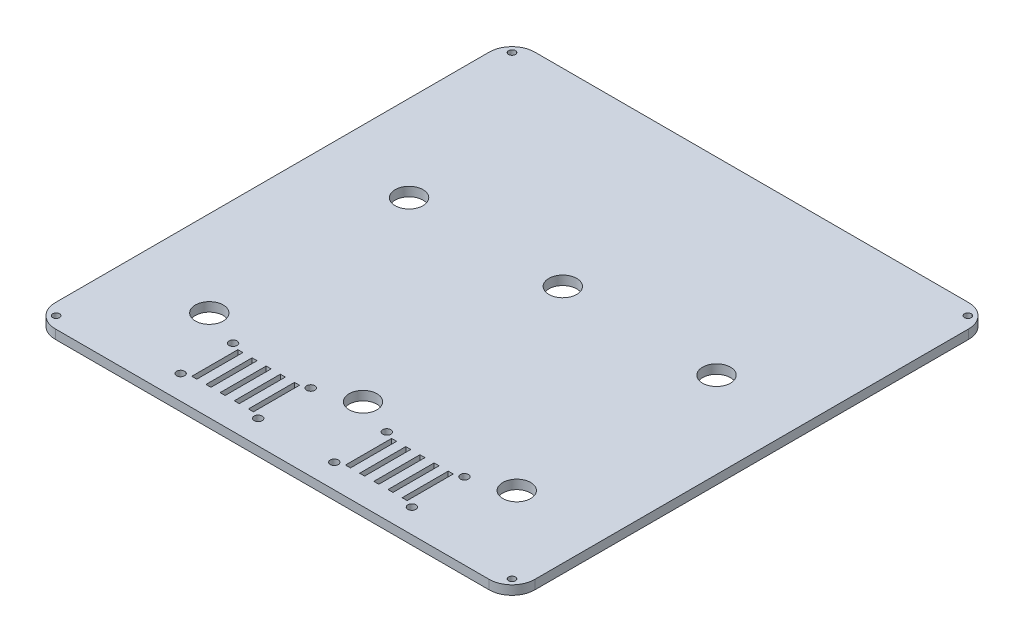
SolidWorks part; units mm, degrees
ref_plane "Front Plane" through (0, 0, 0) normal (0, 0, 1) x (1, 0, 0)
ref_plane "Top Plane" through (0, 0, 0) normal (0, 1, 0) x (1, 0, 0)
ref_plane "Right Plane" through (0, 0, 0) normal (1, 0, 0) x (0, 0, -1)
sketch "Sketch1" plane through (0, 0, 0) normal (0, 1, 0) x (1, 0, 0)
  line L0 (-101, -101) -> (-101, 101)
  line L5 (-105, -105) -> (105, -105)
  line L6 (-105, -105) -> (-105, 105)
  line L7 (-105, 105) -> (105, 105)
  line L8 (105, -105) -> (105, 105)
  line L9 (-101, 101) -> (101, 101)
  line L10 (101, -101) -> (101, 101)
  line L11 (-101, -101) -> (101, -101)
  line L12 (-101, 101) -> (-99.8333, 99.8333) construction
  line L13 (-55, 0) -> (55, 0) construction
  line L14 (-101, -101) -> (-99.8333, -99.8333) construction
  line L15 (0, -55) -> (0, 55) construction
  line L16 (101, -101) -> (99.8333, -99.8333) construction
  line L17 (101, 101) -> (99.8333, 99.8333) construction
  line L18 (0, 101) -> (0, -101) construction
  line L19 (-67.3333, -65.25) -> (0, -65.25) construction
  line L20 (-67.3333, -65.25) -> (-101, -65.25) construction
  line L21 (-33.6667, 101) -> (-33.6667, -101) construction
  line L22 (-67.3333, 101) -> (-67.3333, -101) construction
  line L23 (-67.3333, -51) -> (-33.6667, -51) construction
  line L24 (-33.6667, -51) -> (0, -51) construction
  line L25 (7.6667, -33) -> (7.6667, -10) construction
  line L26 (67.3333, 13.5) -> (67.3333, -56.5) construction
  line L27 (67.3333, 31) -> (67.3333, 101) construction
  line L29 (-53.6667, -97) -> (-13.6667, -97) construction
  line L30 (-53.6667, -97) -> (-53.6667, -69) construction
  line L31 (-53.6667, -69) -> (-13.6667, -69) construction
  line L32 (-13.6667, -97) -> (-13.6667, -69) construction
  line L33 (-59.6667, -33) -> (-7.6667, -33) construction
  line L34 (-59.6667, -33) -> (-59.6667, -10) construction
  line L35 (-59.6667, -10) -> (-7.6667, -10) construction
  line L36 (-7.6667, -33) -> (-7.6667, -10) construction
  line L40 (59.6667, -33) -> (7.6667, -33) construction
  line L41 (59.6667, -33) -> (59.6667, -10) construction
  line L42 (59.6667, -10) -> (7.6667, -10) construction
  line L43 (-101, -21.5) -> (101, -21.5) construction
  line L44 (-53.6667, -83) -> (-13.6667, -83) construction
  line L45 (-47.1667, -72.9) -> (-44.9667, -72.9)
  line L46 (-47.1667, -72.9) -> (-47.1667, -93.1)
  line L47 (-47.1667, -93.1) -> (-44.9667, -93.1)
  line L48 (-44.9667, -72.9) -> (-44.9667, -93.1)
  line L49 (-40.9667, -72.9) -> (-40.9667, -93.1)
  line L50 (-40.9667, -72.9) -> (-38.7667, -72.9)
  line L51 (-38.7667, -72.9) -> (-38.7667, -93.1)
  line L52 (-40.9667, -93.1) -> (-38.7667, -93.1)
  line L53 (-34.7667, -72.9) -> (-34.7667, -93.1)
  line L54 (-34.7667, -72.9) -> (-32.5667, -72.9)
  line L55 (-32.5667, -72.9) -> (-32.5667, -93.1)
  line L56 (-34.7667, -93.1) -> (-32.5667, -93.1)
  line L57 (-28.5667, -72.9) -> (-28.5667, -93.1)
  line L58 (-28.5667, -72.9) -> (-26.3667, -72.9)
  line L59 (-26.3667, -72.9) -> (-26.3667, -93.1)
  line L60 (-28.5667, -93.1) -> (-26.3667, -93.1)
  line L61 (-22.3667, -72.9) -> (-22.3667, -93.1)
  line L62 (-22.3667, -72.9) -> (-20.1667, -72.9)
  line L63 (-20.1667, -72.9) -> (-20.1667, -93.1)
  line L64 (-22.3667, -93.1) -> (-20.1667, -93.1)
  line L65 (16.6667, -71.5) -> (50.6667, -94.5) construction
  line L66 (-16.6667, -94.5) -> (-50.6667, -94.5) construction
  line L67 (-16.6667, -94.5) -> (-16.6667, -71.5) construction
  line L68 (-16.6667, -71.5) -> (-50.6667, -71.5) construction
  line L69 (-50.6667, -94.5) -> (-50.6667, -71.5) construction
  line L70 (-16.6667, -94.5) -> (-50.6667, -71.5) construction
  line L71 (-16.6667, -71.5) -> (-50.6667, -94.5) construction
  line L72 (16.6667, -94.5) -> (50.6667, -71.5) construction
  line L73 (50.6667, -94.5) -> (50.6667, -71.5) construction
  line L74 (16.6667, -71.5) -> (50.6667, -71.5) construction
  line L75 (16.6667, -94.5) -> (16.6667, -71.5) construction
  line L76 (16.6667, -94.5) -> (50.6667, -94.5) construction
  line L77 (53.6667, -83) -> (13.6667, -83) construction
  line L78 (13.6667, -97) -> (13.6667, -69) construction
  line L79 (53.6667, -69) -> (13.6667, -69) construction
  line L80 (53.6667, -97) -> (53.6667, -69) construction
  line L81 (53.6667, -97) -> (13.6667, -97) construction
  line L82 (22.3667, -93.1) -> (20.1667, -93.1)
  line L83 (20.1667, -72.9) -> (20.1667, -93.1)
  line L84 (22.3667, -72.9) -> (20.1667, -72.9)
  line L85 (22.3667, -72.9) -> (22.3667, -93.1)
  line L86 (28.5667, -93.1) -> (26.3667, -93.1)
  line L87 (26.3667, -72.9) -> (26.3667, -93.1)
  line L88 (28.5667, -72.9) -> (26.3667, -72.9)
  line L89 (28.5667, -72.9) -> (28.5667, -93.1)
  line L90 (34.7667, -93.1) -> (32.5667, -93.1)
  line L91 (32.5667, -72.9) -> (32.5667, -93.1)
  line L92 (34.7667, -72.9) -> (32.5667, -72.9)
  line L93 (34.7667, -72.9) -> (34.7667, -93.1)
  line L94 (40.9667, -93.1) -> (38.7667, -93.1)
  line L95 (38.7667, -72.9) -> (38.7667, -93.1)
  line L96 (40.9667, -72.9) -> (38.7667, -72.9)
  line L97 (40.9667, -72.9) -> (40.9667, -93.1)
  line L98 (44.9667, -72.9) -> (44.9667, -93.1)
  line L99 (47.1667, -93.1) -> (44.9667, -93.1)
  line L100 (47.1667, -72.9) -> (47.1667, -93.1)
  line L101 (47.1667, -72.9) -> (44.9667, -72.9)
  circle A1 centre (-99.8333, 99.8333) radius 1.5
  circle A2 centre (-99.8333, -99.8333) radius 1.5
  circle A3 centre (99.8333, -99.8333) radius 1.5
  circle A4 centre (99.8333, 99.8333) radius 1.5
  circle A5 centre (67.3333, -65.25) radius 8.75 construction
  circle A6 centre (0, -65.25) radius 8.75 construction
  circle A7 centre (-67.3333, -65.25) radius 8.75 construction
  circle A11 centre (67.3333, -65.25) radius 6.1
  circle A12 centre (0, -65.25) radius 6.1
  circle A13 centre (-67.3333, -65.25) radius 6.1
  circle A14 centre (-67.3333, 22.25) radius 6.1
  circle A15 centre (0, 22.25) radius 6.1
  circle A16 centre (67.3333, 22.25) radius 6.1
  circle A17 centre (-67.3333, 22.25) radius 8.75 construction
  circle A18 centre (0, 22.25) radius 8.75 construction
  circle A19 centre (67.3333, 22.25) radius 8.75 construction
  circle A20 centre (-50.6667, -71.5) radius 1.765
  circle A21 centre (-50.6667, -94.5) radius 1.765
  circle A22 centre (-16.6667, -94.5) radius 1.765
  circle A23 centre (-16.6667, -71.5) radius 1.765
  circle A24 centre (16.6667, -71.5) radius 1.765
  circle A25 centre (16.6667, -94.5) radius 1.765
  circle A26 centre (50.6667, -94.5) radius 1.765
  circle A27 centre (50.6667, -71.5) radius 1.765
  point P0 (0, 0)
  point P6 (-105, 0)
  point P7 (0, 105)
  point P27 (-33.6667, -65.25)
  point P62 (-33.6667, -10)
  point P69 (67.3333, -21.5)
  point P70 (59.6667, -21.5)
  point P72 (-33.6667, -69)
  point P85 (-47.1667, -83)
  point P86 (-33.6667, -72.9)
  point P104 (-33.6667, -83)
  point P146 (33.6667, -83)
  dimension "D3" = 4
  dimension "D4" = 3
  dimension "D7" = 8
  dimension "17.5" = 17.5
  dimension "D13" = 28
  dimension "D19" = 12.2
  dimension "D17" = 2.2
  dimension "D24" = 3.53
  dimension "D1" = 210
  dimension "D2" = 210
  dimension "D5" = 1.65
  dimension "D6" = 45
  dimension "D9" = 33.6667
  dimension "D10" = 2
  dimension "D11" = 70
  dimension "D12" = 50
  dimension "D14" = 40
  dimension "D15" = 23
  dimension "D16" = 52
  dimension "D18" = 20.2
  dimension "D20" = 5
  dimension "D21" = 4
  dimension "D22" = 34
  dimension "D23" = 23
  dimension "D8" = 3
extrude "MainExtrude" add sketch "Sketch1" along normal blind 4 contours L10 A4 L9 A1 L0 A2 L11 A3 A16 A15 A14 A13 A12 A11 L64 L61 L62 L63 L60 L57 L58 L59 L56 L53 L54 L55 L52 L49 L50 L51 L45 L48 L47 L46 | L5 L8 L7 L6 L9 A4 L10 A3 L11 A2 L0 A1 | A1 L9 L0 | L11 A2 L0 | A3 L11 L10 | L9 A4 L10
fillet "RoundedCorners" radius 10 4 edges at (-105, 2, -105) (-105, 2, 105) (105, 2, -105) (105, 2, 105)
